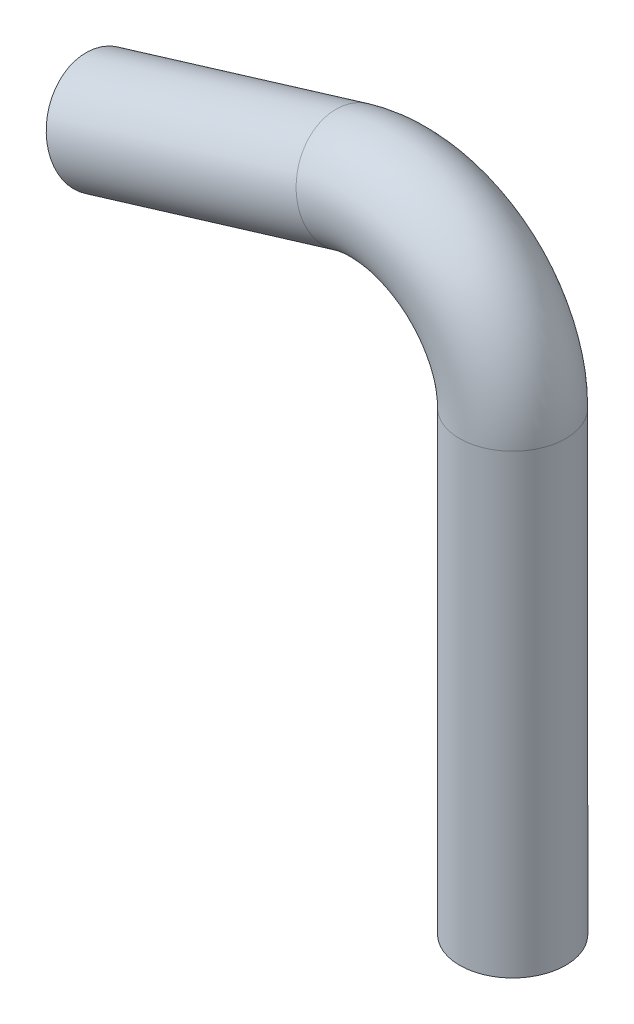
SolidWorks part; units mm, degrees
ref_plane "Front Plane" through (0, 0, 0) normal (0, 0, 1) x (1, 0, 0)
ref_plane "Top Plane" through (0, 0, 0) normal (0, 1, 0) x (1, 0, 0)
ref_plane "Right Plane" through (0, 0, 0) normal (1, 0, 0) x (0, 0, -1)
sketch "Sketch1" plane through (0, 0, 0) normal (0, 1, 0) x (1, 0, 0)
  circle A0 centre (0, 0) radius 21.59
  circle A1 centre (0, 0) radius 19.05
  dimension "D1" = 43.18
  dimension "D2" = 38.1
sketch "Sketch17" plane through (0, 0, 0) normal (0, 0, 1) x (1, 0, 0)
  line L0 (0, 0) -> (0, 185.469)
  line L1 (-65.5703, 234.0744) -> (-167.1703, 203.2)
  line L2 (21.59, 0) -> (-21.59, 0) construction
  arc A0 (0, 185.469) -> (-65.5703, 234.0744) centre (-50.8, 185.469) ccw
  point P6 (0, 254)
  dimension "D3" = 50.8
  dimension "D1" = 101.6
  dimension "D2" = 254
  dimension "D4" = 203.2
sweep "Sweep1" add profiles "Sketch1" path "Sketch17"
equation "\"MDFThickness\"= .2in"
